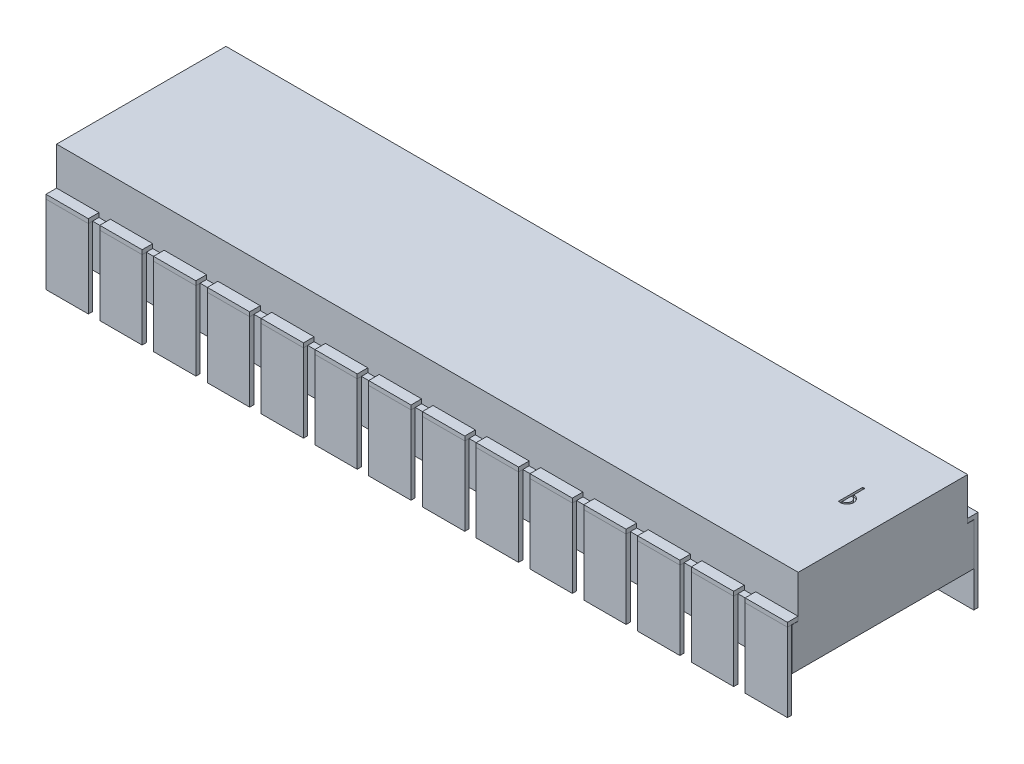
SolidWorks part; units mm, degrees
ref_plane "Front Plane" through (0, 0, 0) normal (0, 0, 1) x (1, 0, 0)
ref_plane "Top Plane" through (0, 0, 0) normal (0, 1, 0) x (1, 0, 0)
ref_plane "Right Plane" through (0, 0, 0) normal (1, 0, 0) x (0, 0, -1)
sketch "Sketch1" plane through (0, 0, 0) normal (0, 1, 0) x (1, 0, 0)
  line L1 (-15.6316, 4.6598) -> (19.3984, 4.6598)
  line L2 (-15.6316, 4.6598) -> (-15.6316, -3.9402)
  line L3 (-15.6316, -3.9402) -> (19.3984, -3.9402)
  line L4 (19.3984, 4.6598) -> (19.3984, -3.9402)
  dimension "D1" = 35.03
  dimension "D2" = 8.6
extrude "Boss-Extrude1" add sketch "Sketch1" along normal blind 2
sketch "Sketch2" plane through (0, 2, 0) normal (0, 1, 0) x (1, 0, 0)
  line L0 (-15.6316, 4.6598) -> (-15.6316, -3.9402) construction
  line L1 (-15.6316, 4.3598) -> (19.3984, 4.3598)
  line L2 (-15.6316, 4.3598) -> (-15.6316, -3.6402)
  line L3 (-15.6316, -3.6402) -> (19.3984, -3.6402)
  line L4 (19.3984, 4.3598) -> (19.3984, -3.6402)
  line L5 (19.3984, -3.9402) -> (19.3984, 4.6598) construction
  line L6 (19.3984, 4.6598) -> (-15.6316, 4.6598) construction
  line L7 (-15.6316, -3.9402) -> (19.3984, -3.9402) construction
  dimension "D1" = 0.3
  dimension "D2" = 0.3
extrude "Boss-Extrude2" add sketch "Sketch2" along normal blind 2
sketch "Sketch4" plane through (0, 4, 0) normal (0, 1, 0) x (1, 0, 0)
  line L0 (17.4422, 1.3636) -> (17.4422, 0.2095)
  line L1 (17.4422, 1.3636) -> (17.5401, 1.3636)
  line L2 (17.5401, 1.3636) -> (17.5401, 0.8356)
  line L3 (17.4912, 0.2095) -> (17.4422, 0.2095)
  line L4 (17.5401, 0.7317) -> (17.5401, 0.2921)
  arc A0 (17.5401, 0.8356) -> (17.4912, 0.2095) centre (17.5401, 0.5207) cw
  arc A1 (17.5401, 0.7317) -> (17.5401, 0.2921) centre (17.5401, 0.5119) cw
extrude "Cut-Extrude2" cut sketch "Sketch4" against normal blind 0.1 contours L3 L0 L1 L2 A0 | A1 L4
sketch "Sketch5" plane through (0, 0, 3.6402) normal (0, 0, 1) x (1, 0, 0)
  line L0 (-13.0916, 2) -> (-13.0916, 2.2)
  line L1 (-15.6316, 2) -> (-13.6316, 2)
  line L2 (-15.6316, 2) -> (-15.6316, 2.2)
  line L3 (-15.6316, 2.2) -> (-13.6316, 2.2)
  line L4 (-13.6316, 2) -> (-13.6316, 2.2)
  line L5 (-13.0916, 2) -> (-11.0916, 2)
  line L6 (-11.0916, 2) -> (-11.0916, 2.2)
  line L7 (-13.0916, 2.2) -> (-11.0916, 2.2)
  line L8 (-10.5516, 2) -> (-10.5516, 2.2)
  line L9 (-10.5516, 2) -> (-8.5516, 2)
  line L10 (-8.5516, 2) -> (-8.5516, 2.2)
  line L11 (-10.5516, 2.2) -> (-8.5516, 2.2)
  line L12 (-8.0116, 2) -> (-8.0116, 2.2)
  line L13 (-8.0116, 2) -> (-6.0116, 2)
  line L14 (-6.0116, 2) -> (-6.0116, 2.2)
  line L15 (-8.0116, 2.2) -> (-6.0116, 2.2)
  line L16 (-5.4716, 2) -> (-5.4716, 2.2)
  line L17 (-5.4716, 2) -> (-3.4716, 2)
  line L18 (-3.4716, 2) -> (-3.4716, 2.2)
  line L19 (-5.4716, 2.2) -> (-3.4716, 2.2)
  line L20 (-2.9316, 2) -> (-2.9316, 2.2)
  line L21 (-2.9316, 2) -> (-0.9316, 2)
  line L22 (-0.9316, 2) -> (-0.9316, 2.2)
  line L23 (-2.9316, 2.2) -> (-0.9316, 2.2)
  line L24 (-0.3916, 2) -> (-0.3916, 2.2)
  line L25 (-0.3916, 2) -> (1.6084, 2)
  line L26 (1.6084, 2) -> (1.6084, 2.2)
  line L27 (-0.3916, 2.2) -> (1.6084, 2.2)
  line L28 (2.1484, 2) -> (2.1484, 2.2)
  line L29 (2.1484, 2) -> (4.1484, 2)
  line L30 (4.1484, 2) -> (4.1484, 2.2)
  line L31 (2.1484, 2.2) -> (4.1484, 2.2)
  line L32 (4.6884, 2) -> (4.6884, 2.2)
  line L33 (4.6884, 2) -> (6.6884, 2)
  line L34 (6.6884, 2) -> (6.6884, 2.2)
  line L35 (4.6884, 2.2) -> (6.6884, 2.2)
  line L36 (7.2284, 2) -> (7.2284, 2.2)
  line L37 (7.2284, 2) -> (9.2284, 2)
  line L38 (9.2284, 2) -> (9.2284, 2.2)
  line L39 (7.2284, 2.2) -> (9.2284, 2.2)
  line L40 (9.7684, 2) -> (9.7684, 2.2)
  line L41 (9.7684, 2) -> (11.7684, 2)
  line L42 (11.7684, 2) -> (11.7684, 2.2)
  line L43 (9.7684, 2.2) -> (11.7684, 2.2)
  line L44 (12.3084, 2) -> (12.3084, 2.2)
  line L45 (12.3084, 2) -> (14.3084, 2)
  line L46 (14.3084, 2) -> (14.3084, 2.2)
  line L47 (12.3084, 2.2) -> (14.3084, 2.2)
  line L48 (14.8484, 2) -> (14.8484, 2.2)
  line L49 (14.8484, 2) -> (16.8484, 2)
  line L50 (16.8484, 2) -> (16.8484, 2.2)
  line L51 (14.8484, 2.2) -> (16.8484, 2.2)
  line L52 (17.3884, 2) -> (17.3884, 2.2)
  line L53 (17.3884, 2) -> (19.3884, 2)
  line L54 (19.3884, 2) -> (19.3884, 2.2)
  line L55 (17.3884, 2.2) -> (19.3884, 2.2)
  dimension "D1" = 2
  dimension "D2" = 0.2
  dimension "D3" = 14
extrude "Boss-Extrude3" add sketch "Sketch5" along normal blind 0.5
sketch "Sketch6" plane through (0, 4, 0) normal (0, 1, 0) x (1, 0, 0)
  line L0 (-15.6316, 0.3598) -> (19.3984, 0.3598) construction
  line L1 (-15.6316, 4.3598) -> (-15.6316, -3.6402) construction
  line L2 (19.3984, -3.6402) -> (19.3984, 4.3598) construction
sketch "Sketch7" plane through (0, 0, 4.1402) normal (0, 0, 1) x (1, 0, 0)
  line L0 (-13.0916, 2) -> (-13.0916, -1.7)
  line L2 (-15.6316, 2) -> (-15.6316, -1.7)
  line L3 (-15.6316, -1.7) -> (-13.6316, -1.7)
  line L4 (-13.6316, 2) -> (-13.6316, -1.7)
  line L5 (-13.0916, 2) -> (-11.0916, 2)
  line L6 (-11.0916, 2) -> (-11.0916, -1.7)
  line L7 (-13.0916, -1.7) -> (-11.0916, -1.7)
  line L8 (-10.5516, 2) -> (-10.5516, -1.7)
  line L9 (-10.5516, 2) -> (-8.5516, 2)
  line L10 (-8.5516, 2) -> (-8.5516, -1.7)
  line L11 (-10.5516, -1.7) -> (-8.5516, -1.7)
  line L12 (-8.0116, 2) -> (-8.0116, -1.7)
  line L13 (-8.0116, 2) -> (-6.0116, 2)
  line L14 (-6.0116, 2) -> (-6.0116, -1.7)
  line L15 (-8.0116, -1.7) -> (-6.0116, -1.7)
  line L16 (-5.4716, 2) -> (-5.4716, -1.7)
  line L17 (-5.4716, 2) -> (-3.4716, 2)
  line L18 (-3.4716, 2) -> (-3.4716, -1.7)
  line L19 (-5.4716, -1.7) -> (-3.4716, -1.7)
  line L20 (-2.9316, 2) -> (-2.9316, -1.7)
  line L21 (-2.9316, 2) -> (-0.9316, 2)
  line L22 (-0.9316, 2) -> (-0.9316, -1.7)
  line L23 (-2.9316, -1.7) -> (-0.9316, -1.7)
  line L24 (-0.3916, 2) -> (-0.3916, -1.7)
  line L25 (-0.3916, 2) -> (1.6084, 2)
  line L26 (1.6084, 2) -> (1.6084, -1.7)
  line L27 (-0.3916, -1.7) -> (1.6084, -1.7)
  line L28 (2.1484, 2) -> (2.1484, -1.7)
  line L29 (2.1484, 2) -> (4.1484, 2)
  line L30 (4.1484, 2) -> (4.1484, -1.7)
  line L31 (2.1484, -1.7) -> (4.1484, -1.7)
  line L32 (4.6884, 2) -> (4.6884, -1.7)
  line L33 (4.6884, 2) -> (6.6884, 2)
  line L34 (6.6884, 2) -> (6.6884, -1.7)
  line L35 (4.6884, -1.7) -> (6.6884, -1.7)
  line L36 (7.2284, 2) -> (7.2284, -1.7)
  line L37 (7.2284, 2) -> (9.2284, 2)
  line L38 (9.2284, 2) -> (9.2284, -1.7)
  line L39 (7.2284, -1.7) -> (9.2284, -1.7)
  line L40 (9.7684, 2) -> (9.7684, -1.7)
  line L41 (9.7684, 2) -> (11.7684, 2)
  line L42 (11.7684, 2) -> (11.7684, -1.7)
  line L43 (9.7684, -1.7) -> (11.7684, -1.7)
  line L44 (12.3084, 2) -> (12.3084, -1.7)
  line L45 (12.3084, 2) -> (14.3084, 2)
  line L46 (14.3084, 2) -> (14.3084, -1.7)
  line L47 (12.3084, -1.7) -> (14.3084, -1.7)
  line L48 (14.8484, 2) -> (14.8484, -1.7)
  line L49 (14.8484, 2) -> (16.8484, 2)
  line L50 (16.8484, 2) -> (16.8484, -1.7)
  line L51 (14.8484, -1.7) -> (16.8484, -1.7)
  line L52 (17.3884, 2) -> (17.3884, -1.7)
  line L53 (17.3884, 2) -> (19.3884, 2)
  line L54 (19.3884, 2) -> (19.3884, -1.7)
  line L55 (17.3884, -1.7) -> (19.3884, -1.7)
  line L56 (-15.6316, 2) -> (-15.6316, 2.2)
  line L57 (-15.6316, 2.2) -> (-13.6316, 2.2)
  line L58 (-13.6316, 2.2) -> (-13.6316, 2)
  dimension "D1" = 2
  dimension "D2" = 3.7
  dimension "D3" = 14
extrude "Boss-Extrude4" add sketch "Sketch7" against normal blind 0.2 separate body
ref_plane "Plane1" through (0, 0, -0.3598) normal (0, 0, 1) x (1, 0, 0)
mirror "Mirror1" about plane through (0, 0, -0.3598) normal (0, 0, 1) of "Boss-Extrude3"
mirror "Mirror2" about plane through (0, 0, -0.3598) normal (0, 0, 1) of "Boss-Extrude4"
